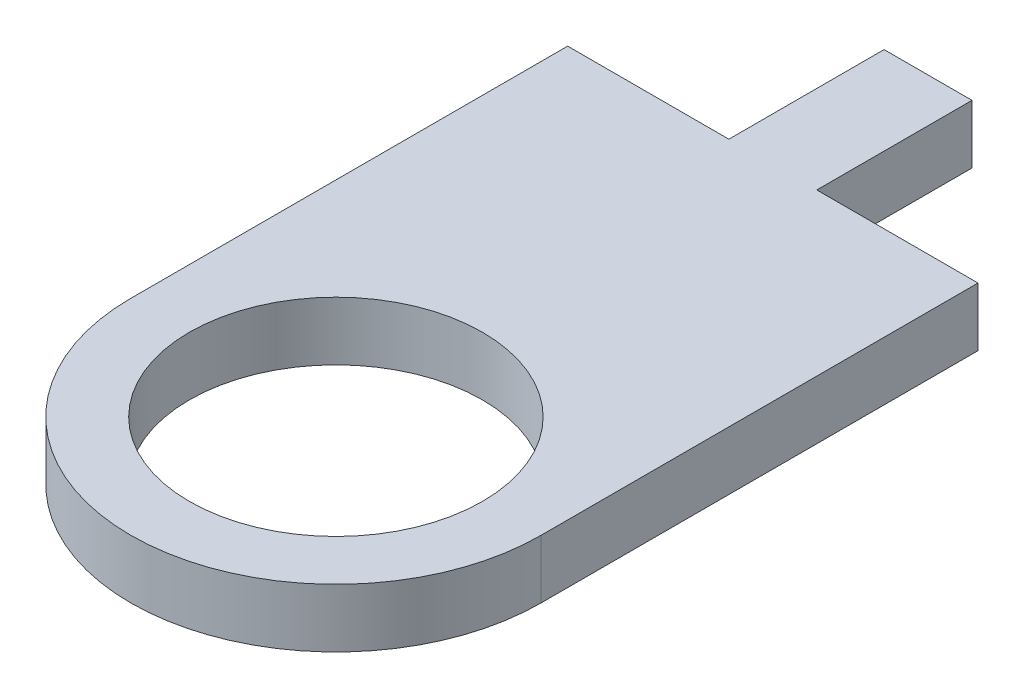
SolidWorks part; units mm, degrees
ref_plane "Front Plane" through (0, 0, 0) normal (0, 0, 1) x (1, 0, 0)
ref_plane "Top Plane" through (0, 0, 0) normal (0, 1, 0) x (1, 0, 0)
ref_plane "Right Plane" through (0, 0, 0) normal (1, 0, 0) x (0, 0, -1)
sketch "Sketch1" plane through (0, 0, 0) normal (0, 1, 0) x (1, 0, 0)
  line L0 (35, 0) -> (35, 74.5346)
  line L1 (-35, 0) -> (-35, 74.5346)
  line L2 (-35, 74.5346) -> (-7.5, 74.5346)
  line L3 (-7.5, 74.5346) -> (-7.5, 101.0116)
  line L4 (-7.5, 101.0116) -> (7.5, 101.0116)
  line L5 (7.5, 101.0116) -> (7.5, 74.5346)
  line L6 (7.5, 74.5346) -> (35, 74.5346)
  circle A0 centre (0, 0) radius 35
  circle A1 centre (0, 0) radius 25
  dimension "D1" = 70
  dimension "D2" = 50
  dimension "D3" = 15
extrude "Boss-Extrude2" add sketch "Sketch1" along normal blind 10 contours A0 A1 | A0 L0 L6 L5 L4 L3 L2 L1
